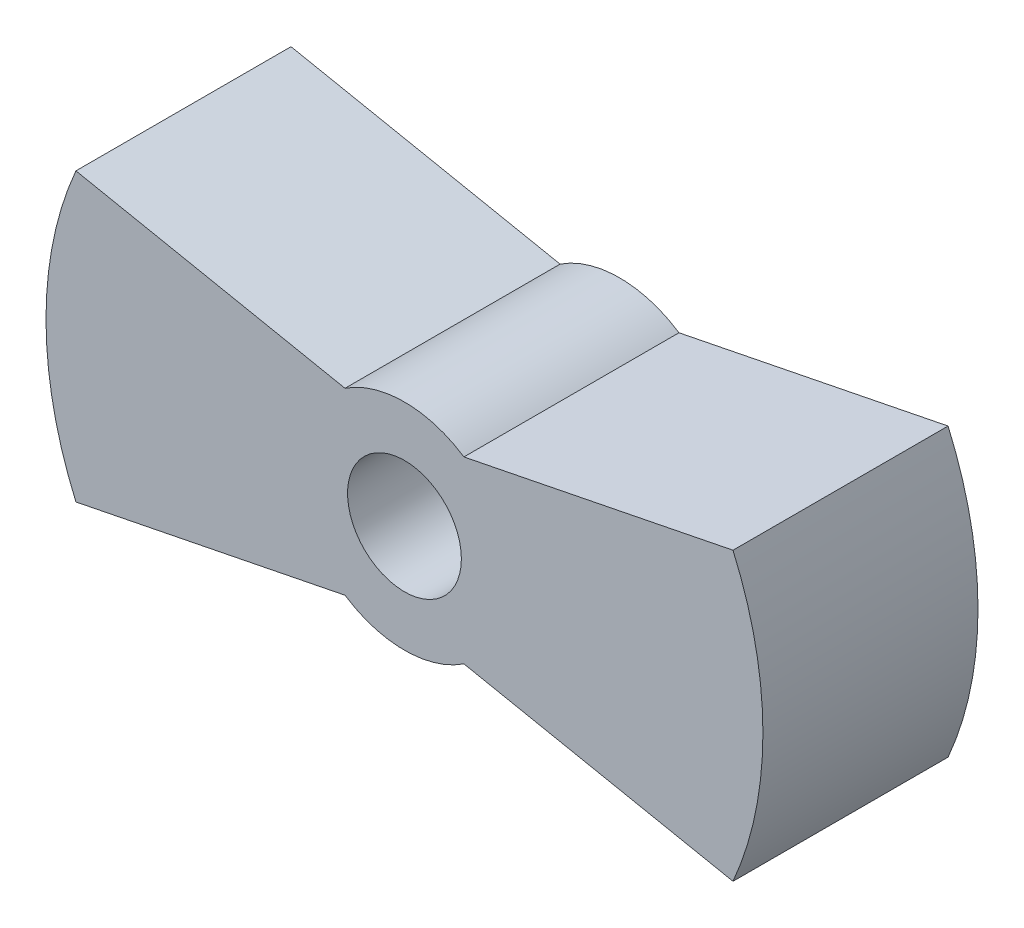
SolidWorks part; units mm, degrees
ref_plane "Front Plane" through (0, 0, 0) normal (0, 0, 1) x (1, 0, 0)
ref_plane "Top Plane" through (0, 0, 0) normal (0, 1, 0) x (1, 0, 0)
ref_plane "Right Plane" through (0, 0, 0) normal (1, 0, 0) x (0, 0, -1)
sketch "Sketch1" plane through (0, 0, 0) normal (0, 0, 1) x (1, 0, 0)
  line L0 (-1.6583, 2.5) -> (-9.1652, 4)
  line L1 (-1.6583, -2.5) -> (-9.1652, -4)
  line L2 (-10, 0) -> (10, 0) construction
  line L3 (0, -3) -> (0, 3) construction
  line L4 (1.6583, -2.5) -> (9.1652, -4)
  line L5 (1.6583, 2.5) -> (9.1652, 4)
  circle A0 centre (0, 0) radius 1.5875
  circle A1 centre (0, 0) radius 3
  arc A2 (-9.1652, 4) -> (-9.1652, -4) centre (0, 0) ccw
  arc A3 (9.1652, -4) -> (9.1652, 4) centre (0, 0) ccw
  dimension "D1" = 3.175
  dimension "D2" = 6
  dimension "D5" = 20
  dimension "D3" = 4
  dimension "D4" = 2.5
extrude "Boss-Extrude1" add sketch "Sketch1" along normal blind 6 contours L0 A2 L1 A1 | A1 A0 | L4 A3 L5 A1
sketch "Sketch2" plane through (0, 0, 0) normal (1, 0, 0) x (0, 0, -1)
  line L0 (-6, 0) -> (0, 0) construction
  line L1 (-6, 4) -> (-6, -4) construction
  line L2 (-3, 2.1) -> (-5.1, 2.1)
  line L3 (-5.1, 2.1) -> (-5.1, -2.1)
  line L4 (-5.1, -2.1) -> (-3, -2.1)
  arc A0 (-3, -2.1) -> (-3, 2.1) centre (-3, 0) ccw
  point P8 (-3, 0)
  dimension "D1" = 4.2
extrude "Cut-Extrude1" cut sketch "Sketch2" against normal blind 2.1 from offset 9
mirror "Mirror1" about plane through (0, 0, 0) normal (1, 0, 0) of "Cut-Extrude1"
